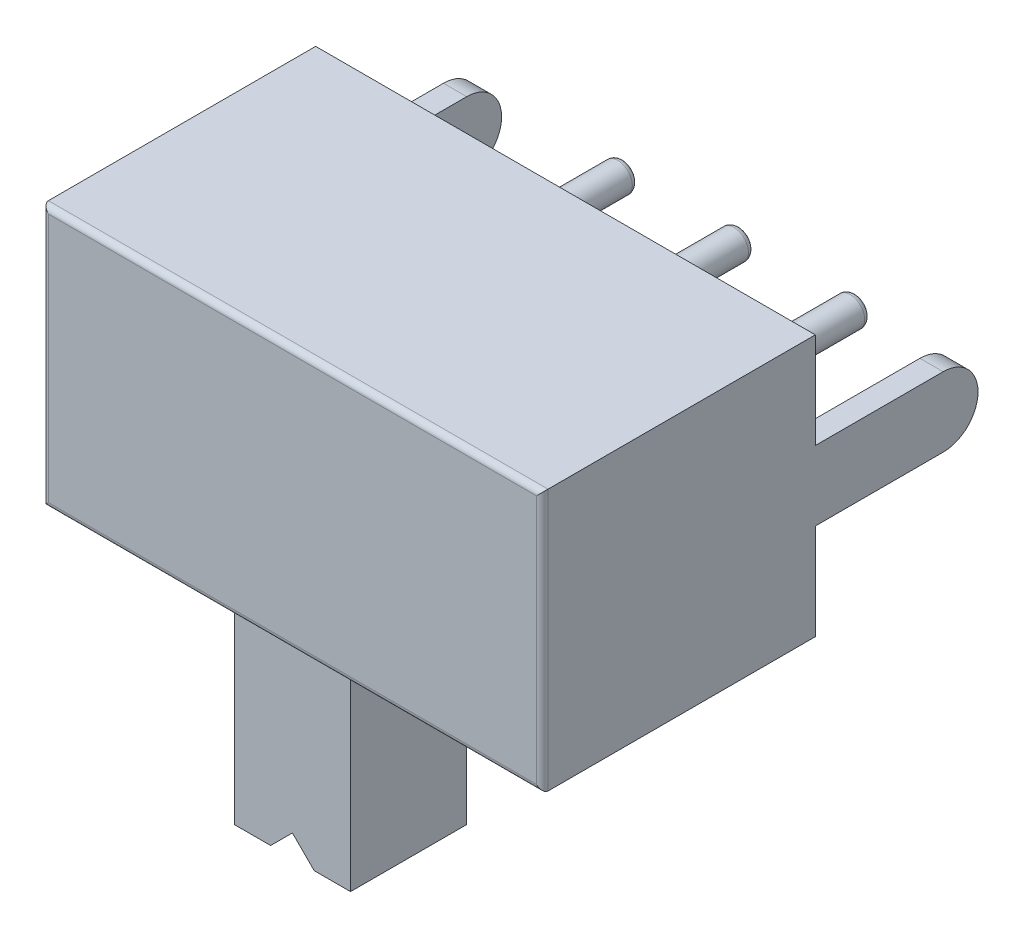
SolidWorks part; units mm, degrees
ref_plane "Front Plane" through (0, 0, 0) normal (0, 0, 1) x (1, 0, 0)
ref_plane "Top Plane" through (0, 0, 0) normal (0, 1, 0) x (1, 0, 0)
ref_plane "Right Plane" through (0, 0, 0) normal (1, 0, 0) x (0, 0, -1)
sketch "Sketch1" plane through (0, 0, 0) normal (0, 0, 1) x (1, 0, 0)
  line L1 (4.3, -2.25) -> (-4.3, -2.25)
  line L2 (4.3, -2.25) -> (4.3, 2.25)
  line L3 (4.3, 2.25) -> (-4.3, 2.25)
  line L4 (-4.3, -2.25) -> (-4.3, 2.25)
  line L5 (4.3, -2.25) -> (-4.3, 2.25) construction
  line L6 (4.3, 2.25) -> (-4.3, -2.25) construction
  point P0 (0, 0)
  dimension "D1" = 4.5
  dimension "D2" = 8.6
extrude "Boss-Extrude1" add sketch "Sketch1" along normal blind 4.7
sketch "Sketch2" plane through (0, -2.25, 0) normal (0, -1, 0) x (1, 0, 0)
  line L0 (-4.3, 4.7) -> (4.3, 4.7) construction
  line L1 (2.05, 1.45) -> (-2.05, 1.45)
  line L2 (2.05, 1.45) -> (2.05, 3.95)
  line L3 (2.05, 3.95) -> (-2.05, 3.95)
  line L4 (-2.05, 1.45) -> (-2.05, 3.95)
  line L5 (2.05, 1.45) -> (-2.05, 3.95) construction
  line L6 (2.05, 3.95) -> (-2.05, 1.45) construction
  point P0 (0, 2.7)
  point P7 (0, 4.7)
  dimension "D1" = 4.1
  dimension "D2" = 2
  dimension "D3" = 2.5
extrude "Cut-Extrude1" cut sketch "Sketch2" against normal blind 0.5
ref_plane "Plane1" through (0, 0, 0) normal (1, 0, 0) x (0, 0, -1)
sketch "Sketch3" plane through (4.3, 0, 0) normal (1, 0, 0) x (0, 0, -1)
  line L0 (0, -0.6) -> (2.2, -0.6)
  line L1 (0, 0.6) -> (2.2, 0.6)
  line L4 (0, -2.25) -> (0, 2.25)
  line L5 (0, 2.25) -> (-4.7, 2.25)
  line L6 (-4.7, 2.25) -> (-4.7, -2.25)
  line L7 (-4.7, -2.25) -> (0, -2.25)
  line L8 (0, -2.25) -> (0, 2.25)
  line L9 (0, 2.25) -> (-4.7, 2.25)
  line L10 (-4.7, 2.25) -> (-4.7, -2.25)
  line L11 (-4.7, -2.25) -> (0, -2.25)
  arc A0 (2.2, -0.6) -> (2.2, 0.6) centre (2.2, 0) ccw
  point P9 (0, 0)
  point P10 (2.8, 0)
  line M7 (0, -2.25) -> (0, 2.25)
  dimension "D2" = 1.2
  dimension "D3" = 0.6
  dimension "D4" = 7.5
  dimension "D1" = 0
extrude "Boss-Extrude2" add sketch "Sketch3" against normal blind 0.4 contours L0 A0 L1 M7
mirror "Mirror1" about plane through (0, 0, 0) normal (1, 0, 0) of "Boss-Extrude2"
sketch "Sketch4" plane through (0, 0, 0) normal (0, 0, -1) x (-1, 0, 0)
  line L12 (4.3, -0.6) -> (3.9, -0.6)
  line L13 (3.9, -0.6) -> (3.9, 0.6)
  line L14 (3.9, 0.6) -> (4.3, 0.6)
  line L15 (4.3, 0.6) -> (4.3, 2.25)
  line L16 (4.3, 2.25) -> (-4.3, 2.25)
  line L17 (-4.3, 2.25) -> (-4.3, 0.6)
  line L18 (-4.3, 0.6) -> (-3.9, 0.6)
  line L19 (-3.9, 0.6) -> (-3.9, -0.6)
  line L20 (-3.9, -0.6) -> (-4.3, -0.6)
  line L21 (-4.3, -0.6) -> (-4.3, -2.25)
  line L22 (-4.3, -2.25) -> (4.3, -2.25)
  line L23 (4.3, -2.25) -> (4.3, -0.6)
  line L24 (4.3, -0.6) -> (3.9, -0.6)
  line L25 (3.9, -0.6) -> (3.9, 0.6)
  line L26 (3.9, 0.6) -> (4.3, 0.6)
  line L27 (4.3, 0.6) -> (4.3, 2.25)
  line L28 (4.3, 2.25) -> (-4.3, 2.25)
  line L29 (-4.3, 2.25) -> (-4.3, 0.6)
  line L30 (-4.3, 0.6) -> (-3.9, 0.6)
  line L31 (-3.9, 0.6) -> (-3.9, -0.6)
  line L32 (-3.9, -0.6) -> (-4.3, -0.6)
  line L33 (-4.3, -0.6) -> (-4.3, -2.25)
  line L34 (-4.3, -2.25) -> (4.3, -2.25)
  line L35 (4.3, -2.25) -> (4.3, -0.6)
  line L36 (3.9, 0) -> (-3.9, 0) construction
  circle A0 centre (2, 0) radius 0.25
  circle A1 centre (0, 0) radius 0.25
  circle A2 centre (-2, 0) radius 0.25
  point P18 (0, -2.25)
  dimension "D1" = 0
  dimension "D2" = 0.5
  dimension "D3" = 2
  dimension "D4" = 2
extrude "Boss-Extrude3" add sketch "Sketch4" along normal blind 3 contours A0 L36 | L36 A0 | L36 A1 | A1 L36 | L36 A2 | A2 L36
sketch "Sketch5" plane through (0, -1.75, 0) normal (0, -1, 0) x (1, 0, 0)
  line L1 (-2, 1.7) -> (0, 1.7)
  line L2 (-2, 1.7) -> (-2, 3.7)
  line L3 (-2, 3.7) -> (0, 3.7)
  line L4 (0, 1.7) -> (0, 3.7)
  line L5 (-2, 1.7) -> (0, 3.7) construction
  line L6 (-2, 3.7) -> (0, 1.7) construction
  line L11 (-2.05, 3.95) -> (-2.05, 1.45)
  line L12 (-2.05, 1.45) -> (2.05, 1.45)
  line L13 (2.05, 1.45) -> (2.05, 3.95)
  line L14 (2.05, 3.95) -> (-2.05, 3.95)
  line L15 (-2.05, 3.95) -> (-2.05, 1.45)
  line L16 (-2.05, 1.45) -> (2.05, 1.45)
  line L17 (2.05, 1.45) -> (2.05, 3.95)
  line L18 (2.05, 3.95) -> (-2.05, 3.95)
  point P0 (-1, 2.7)
  point P5 (-0.9977, 2.6173)
  point P6 (-0.9629, 2.6644)
  point P9 (-1.864, 3.6118)
  point P10 (-2, 2.7)
  point P12 (-2.05, 2.7)
  point P14 (-0.9828, 2.7)
  point P15 (0, 3.95)
  dimension "D1" = 2
  dimension "D2" = 0
extrude "Boss-Extrude4" add sketch "Sketch5" along normal blind 4.6 contours L1 L4 L3 L2
sketch "Sketch6" plane through (0, 0, 3.7) normal (0, 0, 1) x (1, 0, 0)
  line L0 (-1.375, -6.35) -> (-1, -5.975)
  line L1 (-1, -5.975) -> (-0.625, -6.35)
  line L4 (0, -1.75) -> (-2, -1.75)
  line L5 (-2, -1.75) -> (-2, -6.35)
  line L6 (-2, -6.35) -> (0, -6.35)
  line L7 (0, -6.35) -> (0, -1.75)
  line L8 (0, -1.75) -> (-2, -1.75)
  line L9 (-2, -1.75) -> (-2, -6.35)
  line L10 (-2, -6.35) -> (0, -6.35)
  line L11 (0, -6.35) -> (0, -1.75)
  point P6 (-1, -6.35)
  line M9 (-2, -6.35) -> (0, -6.35)
  dimension "D2" = 45
  dimension "D3" = 0.75
  dimension "D1" = 0
extrude "Cut-Extrude2" cut sketch "Sketch6" against normal up to next contours L1 L0 M9
fillet "Fillet2" radius 0.1 7 edges at (-4.3, 0, 4.7) (0, 2.25, 4.7) (4.3, 0, 4.7) (0, -2.25, 4.7) (-2.25, 0, -3) (-0.25, 0, -3) (1.75, 0, -3)
equation "\"D3@Sketch3\"=\"D2@Sketch3\"/2"
equation "\"D4@Sketch4\"=\"D3@Sketch4\""
